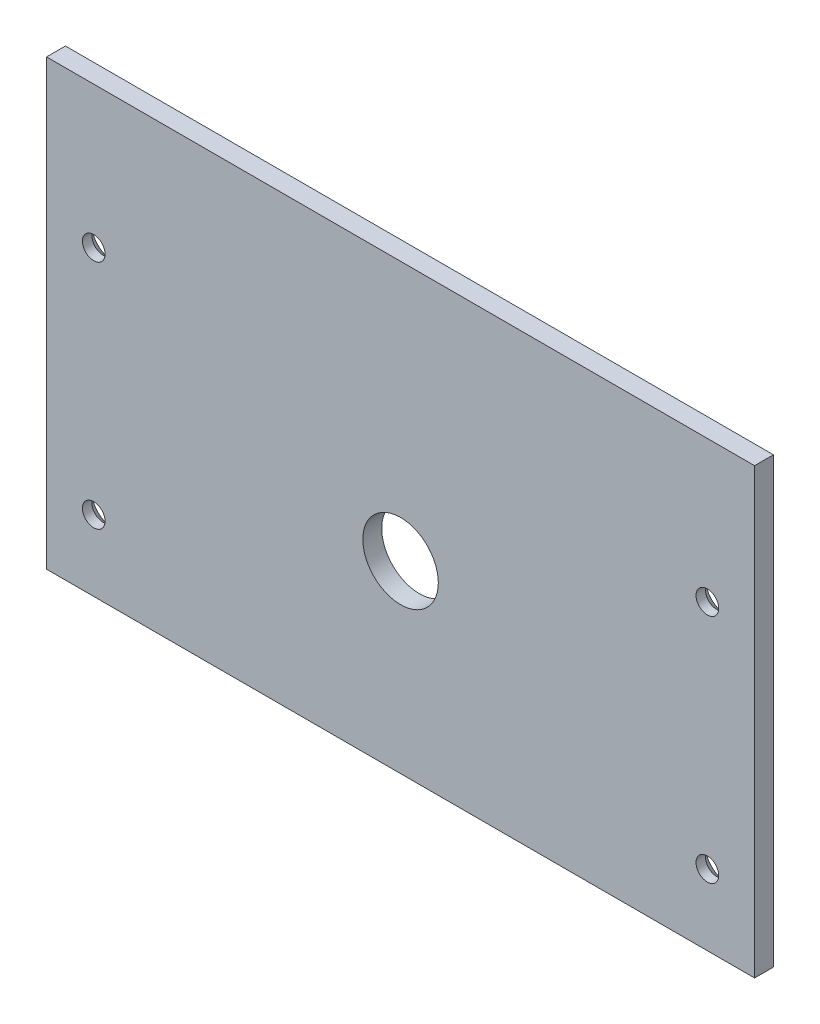
SolidWorks part; units mm, degrees
ref_plane "Front Plane" through (0, 0, 0) normal (0, 0, 1) x (1, 0, 0)
ref_plane "Top Plane" through (0, 0, 0) normal (0, 1, 0) x (1, 0, 0)
ref_plane "Right Plane" through (0, 0, 0) normal (1, 0, 0) x (0, 0, -1)
sketch "Sketch1" plane through (0, 0, 0) normal (0, 0, 1) x (1, 0, 0)
  line L1 (-37.5, 23.5) -> (37.5, 23.5)
  line L2 (-37.5, 23.5) -> (-37.5, -23.5)
  line L3 (-37.5, -23.5) -> (37.5, -23.5)
  line L4 (37.5, 23.5) -> (37.5, -23.5)
  line L5 (-37.5, 23.5) -> (37.5, -23.5) construction
  line L6 (-37.5, -23.5) -> (37.5, 23.5) construction
  point P0 (0, 0)
  dimension "D1" = 75
  dimension "D2" = 47
extrude "Boss-Extrude1" add sketch "Sketch1" along normal blind 2
sketch "Sketch3" plane through (0, 0, 2) normal (0, 0, 1) x (1, 0, 0)
  line L0 (-37.5, -23.5) -> (37.5, -23.5) construction
  line L1 (37.5, -23.5) -> (37.5, 23.5) construction
  circle A0 centre (0, -4) radius 4
  dimension "D1" = 8
  dimension "D2" = 19.5
  dimension "D3" = 37.5
extrude "Cut-Extrude1" cut sketch "Sketch3" against normal blind 5
hole_wizard "CSK for M2 Countersunk Flat Head Screw1" positions "3DSketch1" profile "Sketch5" countersink size "M2" standard "ISO" end condition through all
sketch3d "3DSketch1"
  point P0 (32.5, 8.5, 0)
  point P2 (32.5, -16, 0)
  point P4 (-32.5, 8.5, 0)
  point P6 (-32.5, -16, 0)
  dimension "D1" = 15
  dimension "D2" = 7.5
  dimension "D3" = 5
  dimension "D4" = 5
  dimension "D5" = 15
  dimension "D6" = 5
  dimension "D7" = 5
  dimension "D8" = 7.5
sketch "Sketch5" plane through (32.5, 8.5, 0) normal (1, 0, 0) x (0, 1, 0)
  line L0 (0, 0) -> (0, 2)
  line L1 (0, 2) -> (1.2, 2)
  line L2 (1.2, 2) -> (1.2, 1)
  line L3 (1.2, 1) -> (2.2, 0)
  line L5 (2.2, 0) -> (0, 0)
  line L6 (-1.2, 1) -> (-2.2, 0) construction
  line L11 (0, -6.35) -> (0, 107.95) construction
  dimension "Thru Hole Dia." = 2.4
  dimension "Thru Hole Depth" = 2
  dimension "Near C'Sink Dia." = 4.4
  dimension "Near C'Sink Angle" = 90
